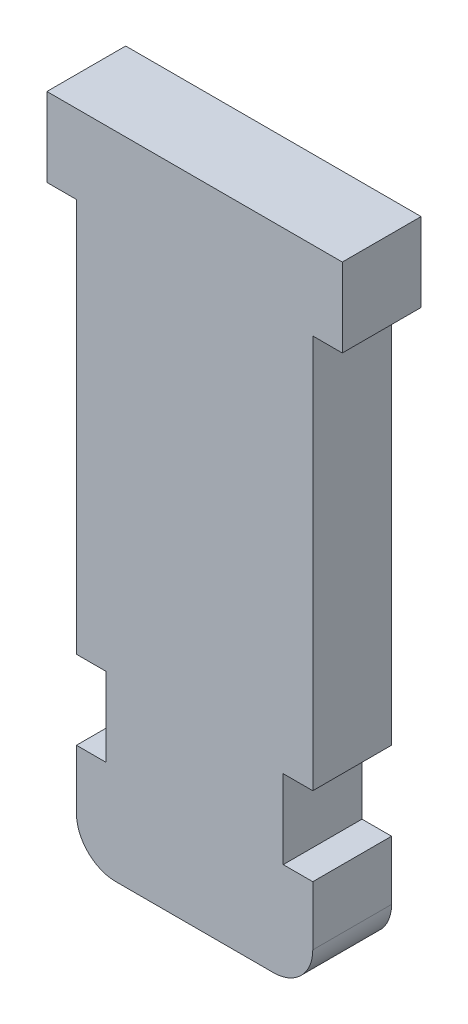
SolidWorks part; units mm, degrees
ref_plane "Ebene vorne" through (0, 0, 0) normal (0, 0, 1) x (1, 0, 0)
ref_plane "Ebene oben" through (0, 0, 0) normal (0, 1, 0) x (1, 0, 0)
ref_plane "Ebene rechts" through (0, 0, 0) normal (1, 0, 0) x (0, 0, -1)
sketch "Skizze1" plane through (0, 0, 0) normal (0, 0, 1) x (1, 0, 0)
  line L0 (6, -31) -> (6, -2)
  line L1 (7.5, -2) -> (-7.5, -2)
  line L2 (7.5, -2) -> (7.5, 2)
  line L3 (7.5, 2) -> (-7.5, 2)
  line L4 (-7.5, -2) -> (-7.5, 2)
  line L5 (7.5, -2) -> (-7.5, 2) construction
  line L6 (7.5, 2) -> (-7.5, -2) construction
  line L7 (6, -31) -> (-6, -31)
  line L8 (6, -2) -> (-6, -2)
  line L9 (-6, -31) -> (-6, -2)
  line L10 (6, -31) -> (-6, -2) construction
  line L11 (6, -2) -> (-6, -31) construction
  point P0 (0, 0)
  point P6 (0, -16.5)
  dimension "D1" = 15
  dimension "D2" = 4
  dimension "D3" = 29
  dimension "D4" = 12
extrude "Aufsatz-Linear austragen1" add sketch "Skizze1" along normal blind 4 contours L9 L7 L0 L1 | L4 L1 L2 L3
sketch "Skizze2" plane through (0, 0, 4) normal (0, 0, 1) x (1, 0, 0)
  line L0 (0, 0) -> (0, -31) construction
  line L1 (6, -31) -> (-6, -31) construction
  line L2 (-6, -31) -> (-6, -2) construction
  line L3 (-6, -22) -> (-4.5, -22)
  line L4 (-6, -22) -> (-6, -26)
  line L5 (-6, -26) -> (-4.5, -26)
  line L6 (-4.5, -22) -> (-4.5, -26)
  line L7 (-6, -2) -> (-7.5, -2) construction
  line L8 (4.5, -22) -> (4.5, -26)
  line L9 (6, -26) -> (4.5, -26)
  line L10 (6, -22) -> (6, -26)
  line L11 (6, -22) -> (4.5, -22)
  dimension "D1" = 4
  dimension "D2" = 1.5
  dimension "D3" = 20
extrude "Schnitt-Linear austragen1" cut sketch "Skizze2" against normal through all
fillet "Verrundung1" radius 2 2 edges at (6, -31, 2) (-6, -31, 2)
